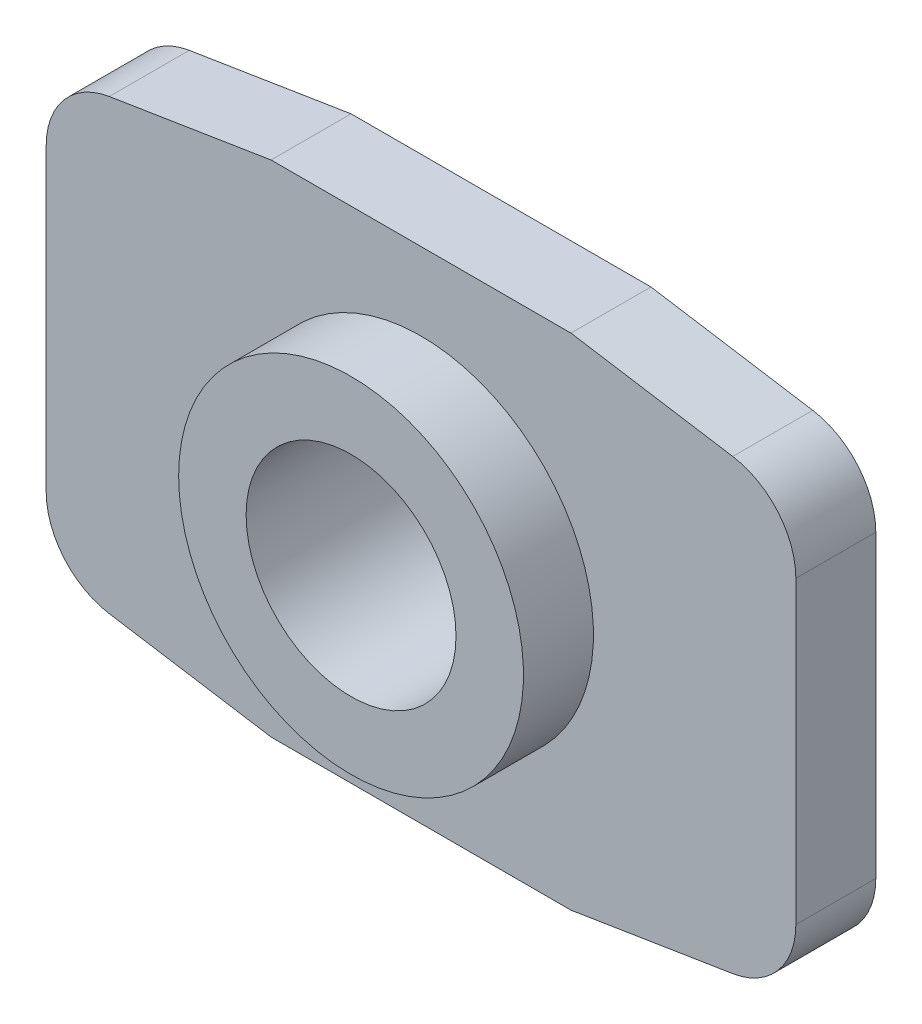
SolidWorks part; units mm, degrees
ref_plane "Front Plane" through (0, 0, 0) normal (0, 0, 1) x (1, 0, 0)
ref_plane "Top Plane" through (0, 0, 0) normal (0, 1, 0) x (1, 0, 0)
ref_plane "Right Plane" through (0, 0, 0) normal (1, 0, 0) x (0, 0, -1)
ref_plane "Plane1" through (0, 0, 1.6) normal (0, 0, 1) x (1, 0, 0)
sketch "Sketch1" plane through (0, 0, 1.6) normal (0, 0, 1) x (1, 0, 0)
  line L0 (3, -5) -> (6.0922, -4.5044)
  line L1 (6.0922, -4.5044) -> (7.5, 4.2787)
  line L2 (7.5, 4.2787) -> (3, 5)
  line L3 (3, 5) -> (-3, 5)
  line L4 (-3, 5) -> (-7.5, 4.2787)
  line L5 (-7.5, 4.2787) -> (-7.5, -4.2787)
  line L6 (-7.5, -4.2787) -> (-3, -5)
  line L7 (-3, -5) -> (3, -5)
extrude "Boss-Extrude1" add sketch "Sketch1" against normal blind 1.6
draft "Draft1" type of draft neutral plane draft angle 9.106 faces to draft 1 face at (6.7961, -0.1128, 0.8) neutral plane through (7.5, 4.2787, 0) neutral plane normal (0.1583, 0.9874, 0) parameters "D1"=9.106
ref_plane "Plane2" through (0, 0, 0) normal (0, -1, 0) x (1, 0, 0)
sketch "Sketch2" plane through (0, 0, 0) normal (0, -1, 0) x (1, 0, 0)
  line L0 (3.45, 3) -> (0, 3)
  line L1 (0, 3) -> (0, 1.6)
  line L2 (0, 1.6) -> (3.45, 1.6)
  line L3 (3.45, 1.6) -> (3.45, 3)
  line L4 (0, 3) -> (0, 1.6) construction
revolve "Revolve1" add sketch "Sketch2" angle 360 about L4
hole_wizard "Hole1" positions "Sketch4" profile "Sketch3" legacy
sketch "Sketch4" plane through (0, 0, 3) normal (0, 0, 1) x (1, 0, 0)
  point P0 (0, 0)
sketch "Sketch3" plane through (0, 0, 3) normal (1, 0, 0) x (0, -1, 0)
  line L0 (0, 0) -> (0, 3)
  line L1 (0, 3) -> (2.1, 3)
  line L2 (2.1, 3) -> (2.1, 0)
  line L3 (2.1, 0) -> (0, 0)
  line L4 (0, 110) -> (0, -10) construction
  dimension "Diameter" = 4.2
  dimension "Depth" = 3
fillet "Fillet1" radius 1.5 4 edges at (7.5, 4.2787, 0.8) (7.5, -4.2787, 0.8) (-7.5, 4.2787, 0.8) (-7.5, -4.2787, 0.8)
